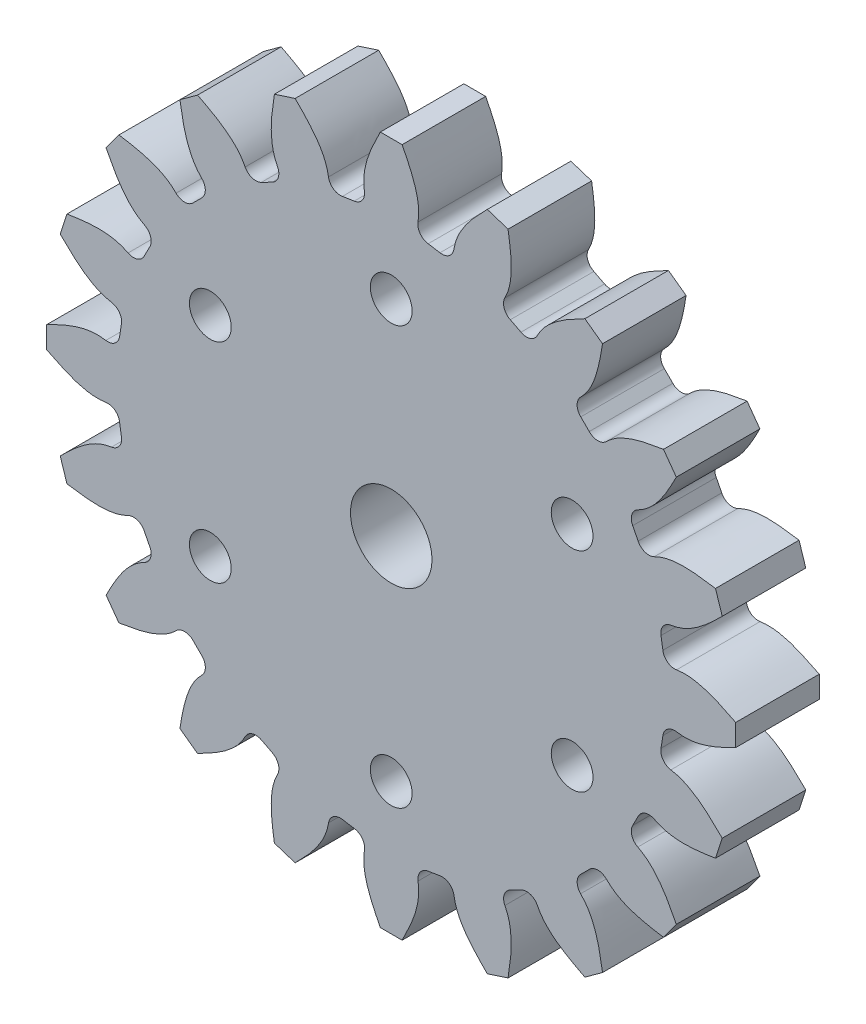
SolidWorks part; units mm, degrees
ref_plane "Plan de face" through (0, 0, 0) normal (0, 0, 1) x (1, 0, 0)
ref_plane "Plan de dessus" through (0, 0, 0) normal (0, 1, 0) x (1, 0, 0)
ref_plane "Plan de droite" through (0, 0, 0) normal (1, 0, 0) x (0, 0, -1)
sketch "Esquisse1" plane through (0, 0, 0) normal (0, 0, 1) x (1, 0, 0)
  line L0 (15.1743, 19.5525) -> (13.9064, 20.4737)
  line L1 (9.3174, 17.3431) -> (8.5503, 17.7339)
  line L2 (8.3896, 23.2847) -> (6.8991, 23.769)
  line L3 (3.5021, 19.3735) -> (2.6518, 19.5081)
  line L4 (0.7836, 24.7376) -> (-0.7836, 24.7376)
  line L5 (-2.656, 19.5075) -> (-3.5064, 19.3727)
  line L6 (-6.8991, 23.769) -> (-8.3896, 23.2847)
  line L7 (-8.5542, 17.732) -> (-9.3212, 17.341)
  line L8 (-13.9064, 20.4737) -> (-15.1743, 19.5525)
  line L9 (-13.615, 14.2207) -> (-14.2237, 13.6119)
  line L10 (-19.5525, 15.1743) -> (-20.4737, 13.9064)
  line L11 (-17.3431, 9.3174) -> (-17.7339, 8.5503)
  line L12 (-23.2847, 8.3896) -> (-23.769, 6.8991)
  line L13 (-19.3735, 3.5021) -> (-19.5081, 2.6518)
  line L14 (-24.7376, 0.7836) -> (-24.7376, -0.7836)
  line L15 (-19.5075, -2.656) -> (-19.3727, -3.5064)
  line L16 (-23.769, -6.8991) -> (-23.2847, -8.3896)
  line L17 (-17.732, -8.5542) -> (-17.341, -9.3212)
  line L18 (-20.4737, -13.9064) -> (-19.5525, -15.1743)
  line L19 (-14.2207, -13.615) -> (-13.6119, -14.2237)
  line L20 (-15.1743, -19.5525) -> (-13.9064, -20.4737)
  line L21 (-9.3174, -17.3431) -> (-8.5503, -17.7339)
  line L22 (-8.3896, -23.2847) -> (-6.8991, -23.769)
  line L23 (-3.5021, -19.3735) -> (-2.6518, -19.5081)
  line L24 (-0.7836, -24.7376) -> (0.7836, -24.7376)
  line L25 (2.656, -19.5075) -> (3.5064, -19.3727)
  line L26 (6.8991, -23.769) -> (8.3896, -23.2847)
  line L27 (8.5542, -17.732) -> (9.3212, -17.341)
  line L28 (13.9064, -20.4737) -> (15.1743, -19.5525)
  line L29 (13.615, -14.2207) -> (14.2237, -13.6119)
  line L30 (19.5525, -15.1743) -> (20.4737, -13.9064)
  line L31 (17.3431, -9.3174) -> (17.7339, -8.5503)
  line L32 (23.2847, -8.3896) -> (23.769, -6.8991)
  line L33 (19.3735, -3.5021) -> (19.5081, -2.6518)
  line L34 (24.7376, -0.7836) -> (24.7376, 0.7836)
  line L35 (19.5075, 2.656) -> (19.3727, 3.5064)
  line L36 (23.769, 6.8991) -> (23.2847, 8.3896)
  line L37 (17.732, 8.5542) -> (17.341, 9.3212)
  line L38 (20.4737, 13.9064) -> (19.5525, 15.1743)
  line L39 (14.2207, 13.615) -> (13.6119, 14.2237)
  arc A7 (3.5021, 19.3735) -> (4.4983, 20.0787) centre (3.6542, 20.2149) ccw
  arc A9 (8.1621, 18.8967) -> (8.5503, 17.7339) centre (8.9216, 18.504) ccw
  arc A11 (9.3174, 17.3431) -> (10.4828, 17.706) centre (9.7221, 18.0963) ccw
  arc A13 (13.602, 15.4496) -> (13.6119, 14.2237) centre (14.203, 14.8414) ccw
  arc A15 (14.2207, 13.615) -> (15.4412, 13.6) centre (14.8383, 14.2063) ccw
  arc A17 (17.7105, 10.4901) -> (17.341, 9.3212) centre (18.0941, 9.7261) ccw
  arc A19 (17.732, 8.5542) -> (18.8881, 8.1628) centre (18.5021, 8.9257) ccw
  arc A21 (20.0853, 4.5039) -> (19.3727, 3.5064) centre (20.2141, 3.6586) ccw
  arc A23 (19.5075, 2.656) -> (20.4861, 1.9265) centre (20.3547, 2.7714) ccw
  arc A25 (20.494, -1.9233) -> (19.5081, -2.6518) centre (20.3553, -2.7669) ccw
  arc A27 (19.3735, -3.5021) -> (20.0787, -4.4983) centre (20.2149, -3.6542) ccw
  arc A29 (18.8967, -8.1621) -> (17.7339, -8.5503) centre (18.504, -8.9216) ccw
  arc A31 (17.3431, -9.3174) -> (17.706, -10.4828) centre (18.0963, -9.7221) ccw
  arc A33 (15.4496, -13.602) -> (14.2237, -13.6119) centre (14.8414, -14.203) ccw
  arc A35 (13.615, -14.2207) -> (13.6, -15.4412) centre (14.2063, -14.8383) ccw
  arc A37 (10.4901, -17.7105) -> (9.3212, -17.341) centre (9.7261, -18.0941) ccw
  arc A39 (8.5542, -17.732) -> (8.1628, -18.8881) centre (8.9257, -18.5021) ccw
  arc A41 (4.5039, -20.0853) -> (3.5064, -19.3727) centre (3.6586, -20.2141) ccw
  arc A43 (2.656, -19.5075) -> (1.9265, -20.4861) centre (2.7714, -20.3547) ccw
  arc A45 (-1.9233, -20.494) -> (-2.6518, -19.5081) centre (-2.7669, -20.3553) ccw
  arc A47 (-3.5021, -19.3735) -> (-4.4983, -20.0787) centre (-3.6542, -20.2149) ccw
  arc A49 (-8.1621, -18.8967) -> (-8.5503, -17.7339) centre (-8.9216, -18.504) ccw
  arc A51 (-9.3174, -17.3431) -> (-10.4828, -17.706) centre (-9.7221, -18.0963) ccw
  arc A53 (-13.602, -15.4496) -> (-13.6119, -14.2237) centre (-14.203, -14.8414) ccw
  arc A55 (-14.2207, -13.615) -> (-15.4412, -13.6) centre (-14.8383, -14.2063) ccw
  arc A57 (-17.7105, -10.4901) -> (-17.341, -9.3212) centre (-18.0941, -9.7261) ccw
  arc A59 (-17.732, -8.5542) -> (-18.8881, -8.1628) centre (-18.5021, -8.9257) ccw
  arc A61 (-20.0853, -4.5039) -> (-19.3727, -3.5064) centre (-20.2141, -3.6586) ccw
  arc A63 (-19.5075, -2.656) -> (-20.4861, -1.9265) centre (-20.3547, -2.7714) ccw
  arc A65 (-20.494, 1.9233) -> (-19.5081, 2.6518) centre (-20.3553, 2.7669) ccw
  arc A67 (-19.3735, 3.5021) -> (-20.0787, 4.4983) centre (-20.2149, 3.6542) ccw
  arc A69 (-18.8967, 8.1621) -> (-17.7339, 8.5503) centre (-18.504, 8.9216) ccw
  arc A71 (-17.3431, 9.3174) -> (-17.706, 10.4828) centre (-18.0963, 9.7221) ccw
  arc A73 (-15.4496, 13.602) -> (-14.2237, 13.6119) centre (-14.8414, 14.203) ccw
  arc A75 (-13.615, 14.2207) -> (-13.6, 15.4412) centre (-14.2063, 14.8383) ccw
  arc A77 (-10.4901, 17.7105) -> (-9.3212, 17.341) centre (-9.7261, 18.0941) ccw
  arc A79 (-8.5542, 17.732) -> (-8.1628, 18.8881) centre (-8.9257, 18.5021) ccw
  arc A81 (-4.5039, 20.0853) -> (-3.5064, 19.3727) centre (-3.6586, 20.2141) ccw
  arc A83 (-2.656, 19.5075) -> (-1.9265, 20.4861) centre (-2.7714, 20.3547) ccw
  arc A85 (1.9233, 20.494) -> (2.6518, 19.5081) centre (2.7669, 20.3553) ccw
  spline S0 degree 3 poles (8.1621, 18.8967) (8.2478, 19.0624) (8.5054, 19.6524) (8.7113, 21.1682) (8.5154, 22.4568) (8.3896, 23.2847) knots 0.425084 0.425084 0.425084 0.425084 0.498147 0.677544 1 1 1 1
  spline S1 degree 3 poles (6.8991, 23.769) (6.3099, 23.1731) (5.3928, 22.2457) (4.6724, 20.8967) (4.5284, 20.2654) (4.4983, 20.0787) knots 0 0 0 0 0.322456 0.501853 0.575753 0.575753 0.575753 0.575753
  spline S2 degree 3 poles (13.602, 15.4496) (13.7347, 15.5807) (14.1621, 16.0622) (14.8262, 17.4402) (15.0382, 18.7262) (15.1743, 19.5525) knots 0.425084 0.425084 0.425084 0.425084 0.498147 0.677544 1 1 1 1
  spline S3 degree 3 poles (13.9064, 20.4737) (13.1619, 20.0891) (12.0032, 19.4904) (10.9011, 18.4301) (10.5691, 17.8742) (10.4828, 17.706) knots 0 0 0 0 0.322456 0.501853 0.575753 0.575753 0.575753 0.575753
  spline S4 degree 3 poles (17.7105, 10.4901) (17.8772, 10.5738) (18.4324, 10.8998) (19.4899, 12.0051) (20.0889, 13.1626) (20.4737, 13.9064) knots 0.425084 0.425084 0.425084 0.425084 0.498147 0.677544 1 1 1 1
  spline S5 degree 3 poles (19.5525, 15.1743) (18.7256, 15.0386) (17.4386, 14.8273) (16.0628, 14.1594) (15.5753, 13.7333) (15.4412, 13.6) knots 0 0 0 0 0.322456 0.501853 0.575753 0.575753 0.575753 0.575753
  spline S6 degree 3 poles (20.0853, 4.5039) (20.2697, 4.532) (20.8985, 4.6704) (22.2458, 5.3948) (23.1731, 6.3106) (23.769, 6.8991) knots 0.425084 0.425084 0.425084 0.425084 0.498147 0.677544 1 1 1 1
  spline S7 degree 3 poles (23.2847, 8.3896) (22.4563, 8.516) (21.1669, 8.7128) (19.6521, 8.5028) (19.0568, 8.2482) (18.8881, 8.1628) knots 0 0 0 0 0.322456 0.501853 0.575753 0.575753 0.575753 0.575753
  spline S8 degree 3 poles (20.494, -1.9233) (20.6781, -1.9535) (21.3189, -2.0162) (22.8241, -1.7436) (23.9891, -1.1591) (24.7376, -0.7836) knots 0.425084 0.425084 0.425084 0.425084 0.498147 0.677544 1 1 1 1
  spline S9 degree 3 poles (24.7376, 0.7836) (23.9888, 1.1598) (22.8234, 1.7454) (21.3178, 2.0138) (20.6729, 1.9556) (20.4861, 1.9265) knots 0 0 0 0 0.322456 0.501853 0.575753 0.575753 0.575753 0.575753
  spline S10 degree 3 poles (18.8967, -8.1621) (19.0624, -8.2478) (19.6524, -8.5054) (21.1682, -8.7113) (22.4568, -8.5154) (23.2847, -8.3896) knots 0.425084 0.425084 0.425084 0.425084 0.498147 0.677544 1 1 1 1
  spline S11 degree 3 poles (23.769, -6.8991) (23.1731, -6.3099) (22.2457, -5.3928) (20.8967, -4.6724) (20.2654, -4.5284) (20.0787, -4.4983) knots 0 0 0 0 0.322456 0.501853 0.575753 0.575753 0.575753 0.575753
  spline S12 degree 3 poles (15.4496, -13.602) (15.5807, -13.7347) (16.0622, -14.1621) (17.4402, -14.8262) (18.7262, -15.0382) (19.5525, -15.1743) knots 0.425084 0.425084 0.425084 0.425084 0.498147 0.677544 1 1 1 1
  spline S13 degree 3 poles (20.4737, -13.9064) (20.0891, -13.1619) (19.4904, -12.0032) (18.4301, -10.9011) (17.8742, -10.5691) (17.706, -10.4828) knots 0 0 0 0 0.322456 0.501853 0.575753 0.575753 0.575753 0.575753
  spline S14 degree 3 poles (10.4901, -17.7105) (10.5738, -17.8772) (10.8998, -18.4324) (12.0051, -19.4899) (13.1626, -20.0889) (13.9064, -20.4737) knots 0.425084 0.425084 0.425084 0.425084 0.498147 0.677544 1 1 1 1
  spline S15 degree 3 poles (15.1743, -19.5525) (15.0386, -18.7256) (14.8273, -17.4386) (14.1594, -16.0628) (13.7333, -15.5753) (13.6, -15.4412) knots 0 0 0 0 0.322456 0.501853 0.575753 0.575753 0.575753 0.575753
  spline S16 degree 3 poles (4.5039, -20.0853) (4.532, -20.2697) (4.6704, -20.8985) (5.3948, -22.2458) (6.3106, -23.1731) (6.8991, -23.769) knots 0.425084 0.425084 0.425084 0.425084 0.498147 0.677544 1 1 1 1
  spline S17 degree 3 poles (8.3896, -23.2847) (8.516, -22.4563) (8.7128, -21.1669) (8.5028, -19.6521) (8.2482, -19.0568) (8.1628, -18.8881) knots 0 0 0 0 0.322456 0.501853 0.575753 0.575753 0.575753 0.575753
  spline S18 degree 3 poles (-1.9233, -20.494) (-1.9535, -20.6781) (-2.0162, -21.3189) (-1.7436, -22.8241) (-1.1591, -23.9891) (-0.7836, -24.7376) knots 0.425084 0.425084 0.425084 0.425084 0.498147 0.677544 1 1 1 1
  spline S19 degree 3 poles (0.7836, -24.7376) (1.1598, -23.9888) (1.7454, -22.8234) (2.0138, -21.3178) (1.9556, -20.6729) (1.9265, -20.4861) knots 0 0 0 0 0.322456 0.501853 0.575753 0.575753 0.575753 0.575753
  spline S20 degree 3 poles (-8.1621, -18.8967) (-8.2478, -19.0624) (-8.5054, -19.6524) (-8.7113, -21.1682) (-8.5154, -22.4568) (-8.3896, -23.2847) knots 0.425084 0.425084 0.425084 0.425084 0.498147 0.677544 1 1 1 1
  spline S21 degree 3 poles (-6.8991, -23.769) (-6.3099, -23.1731) (-5.3928, -22.2457) (-4.6724, -20.8967) (-4.5284, -20.2654) (-4.4983, -20.0787) knots 0 0 0 0 0.322456 0.501853 0.575753 0.575753 0.575753 0.575753
  spline S22 degree 3 poles (-13.602, -15.4496) (-13.7347, -15.5807) (-14.1621, -16.0622) (-14.8262, -17.4402) (-15.0382, -18.7262) (-15.1743, -19.5525) knots 0.425084 0.425084 0.425084 0.425084 0.498147 0.677544 1 1 1 1
  spline S23 degree 3 poles (-13.9064, -20.4737) (-13.1619, -20.0891) (-12.0032, -19.4904) (-10.9011, -18.4301) (-10.5691, -17.8742) (-10.4828, -17.706) knots 0 0 0 0 0.322456 0.501853 0.575753 0.575753 0.575753 0.575753
  spline S24 degree 3 poles (-17.7105, -10.4901) (-17.8772, -10.5738) (-18.4324, -10.8998) (-19.4899, -12.0051) (-20.0889, -13.1626) (-20.4737, -13.9064) knots 0.425084 0.425084 0.425084 0.425084 0.498147 0.677544 1 1 1 1
  spline S25 degree 3 poles (-19.5525, -15.1743) (-18.7256, -15.0386) (-17.4386, -14.8273) (-16.0628, -14.1594) (-15.5753, -13.7333) (-15.4412, -13.6) knots 0 0 0 0 0.322456 0.501853 0.575753 0.575753 0.575753 0.575753
  spline S26 degree 3 poles (-20.0853, -4.5039) (-20.2697, -4.532) (-20.8985, -4.6704) (-22.2458, -5.3948) (-23.1731, -6.3106) (-23.769, -6.8991) knots 0.425084 0.425084 0.425084 0.425084 0.498147 0.677544 1 1 1 1
  spline S27 degree 3 poles (-23.2847, -8.3896) (-22.4563, -8.516) (-21.1669, -8.7128) (-19.6521, -8.5028) (-19.0568, -8.2482) (-18.8881, -8.1628) knots 0 0 0 0 0.322456 0.501853 0.575753 0.575753 0.575753 0.575753
  spline S28 degree 3 poles (-20.494, 1.9233) (-20.6781, 1.9535) (-21.3189, 2.0162) (-22.8241, 1.7436) (-23.9891, 1.1591) (-24.7376, 0.7836) knots 0.425084 0.425084 0.425084 0.425084 0.498147 0.677544 1 1 1 1
  spline S29 degree 3 poles (-24.7376, -0.7836) (-23.9888, -1.1598) (-22.8234, -1.7454) (-21.3178, -2.0138) (-20.6729, -1.9556) (-20.4861, -1.9265) knots 0 0 0 0 0.322456 0.501853 0.575753 0.575753 0.575753 0.575753
  spline S30 degree 3 poles (-18.8967, 8.1621) (-19.0624, 8.2478) (-19.6524, 8.5054) (-21.1682, 8.7113) (-22.4568, 8.5154) (-23.2847, 8.3896) knots 0.425084 0.425084 0.425084 0.425084 0.498147 0.677544 1 1 1 1
  spline S31 degree 3 poles (-23.769, 6.8991) (-23.1731, 6.3099) (-22.2457, 5.3928) (-20.8967, 4.6724) (-20.2654, 4.5284) (-20.0787, 4.4983) knots 0 0 0 0 0.322456 0.501853 0.575753 0.575753 0.575753 0.575753
  spline S32 degree 3 poles (-15.4496, 13.602) (-15.5807, 13.7347) (-16.0622, 14.1621) (-17.4402, 14.8262) (-18.7262, 15.0382) (-19.5525, 15.1743) knots 0.425084 0.425084 0.425084 0.425084 0.498147 0.677544 1 1 1 1
  spline S33 degree 3 poles (-20.4737, 13.9064) (-20.0891, 13.1619) (-19.4904, 12.0032) (-18.4301, 10.9011) (-17.8742, 10.5691) (-17.706, 10.4828) knots 0 0 0 0 0.322456 0.501853 0.575753 0.575753 0.575753 0.575753
  spline S34 degree 3 poles (-10.4901, 17.7105) (-10.5738, 17.8772) (-10.8998, 18.4324) (-12.0051, 19.4899) (-13.1626, 20.0889) (-13.9064, 20.4737) knots 0.425084 0.425084 0.425084 0.425084 0.498147 0.677544 1 1 1 1
  spline S35 degree 3 poles (-15.1743, 19.5525) (-15.0386, 18.7256) (-14.8273, 17.4386) (-14.1594, 16.0628) (-13.7333, 15.5753) (-13.6, 15.4412) knots 0 0 0 0 0.322456 0.501853 0.575753 0.575753 0.575753 0.575753
  spline S36 degree 3 poles (-4.5039, 20.0853) (-4.532, 20.2697) (-4.6704, 20.8985) (-5.3948, 22.2458) (-6.3106, 23.1731) (-6.8991, 23.769) knots 0.425084 0.425084 0.425084 0.425084 0.498147 0.677544 1 1 1 1
  spline S37 degree 3 poles (-8.3896, 23.2847) (-8.516, 22.4563) (-8.7128, 21.1669) (-8.5028, 19.6521) (-8.2482, 19.0568) (-8.1628, 18.8881) knots 0 0 0 0 0.322456 0.501853 0.575753 0.575753 0.575753 0.575753
  spline S38 degree 3 poles (1.9233, 20.494) (1.9535, 20.6781) (2.0162, 21.3189) (1.7436, 22.8241) (1.1591, 23.9891) (0.7836, 24.7376) knots 0.425084 0.425084 0.425084 0.425084 0.498147 0.677544 1 1 1 1
  spline S39 degree 3 poles (-0.7836, 24.7376) (-1.1598, 23.9888) (-1.7454, 22.8234) (-2.0138, 21.3178) (-1.9556, 20.6729) (-1.9265, 20.4861) knots 0 0 0 0 0.322456 0.501853 0.575753 0.575753 0.575753 0.575753
  spline S40 degree 3 poles (6.8991, 23.769) (6.3099, 23.1731) (5.3928, 22.2457) (4.6724, 20.8967) (4.5284, 20.2654) (4.4983, 20.0787) knots 0 0 0 0 0.322456 0.501853 0.575753 0.575753 0.575753 0.575753
  spline S41 degree 3 poles (8.1621, 18.8967) (8.2478, 19.0624) (8.5054, 19.6524) (8.7113, 21.1682) (8.5154, 22.4568) (8.3896, 23.2847) knots 0.425084 0.425084 0.425084 0.425084 0.498147 0.677544 1 1 1 1
  spline S42 degree 3 poles (13.9064, 20.4737) (13.1619, 20.0891) (12.0032, 19.4904) (10.9011, 18.4301) (10.5691, 17.8742) (10.4828, 17.706) knots 0 0 0 0 0.322456 0.501853 0.575753 0.575753 0.575753 0.575753
  spline S43 degree 3 poles (13.602, 15.4496) (13.7347, 15.5807) (14.1621, 16.0622) (14.8262, 17.4402) (15.0382, 18.7262) (15.1743, 19.5525) knots 0.425084 0.425084 0.425084 0.425084 0.498147 0.677544 1 1 1 1
  spline S44 degree 3 poles (19.5525, 15.1743) (18.7256, 15.0386) (17.4386, 14.8273) (16.0628, 14.1594) (15.5753, 13.7333) (15.4412, 13.6) knots 0 0 0 0 0.322456 0.501853 0.575753 0.575753 0.575753 0.575753
  spline S45 degree 3 poles (17.7105, 10.4901) (17.8772, 10.5738) (18.4324, 10.8998) (19.4899, 12.0051) (20.0889, 13.1626) (20.4737, 13.9064) knots 0.425084 0.425084 0.425084 0.425084 0.498147 0.677544 1 1 1 1
  spline S46 degree 3 poles (23.2847, 8.3896) (22.4563, 8.516) (21.1669, 8.7128) (19.6521, 8.5028) (19.0568, 8.2482) (18.8881, 8.1628) knots 0 0 0 0 0.322456 0.501853 0.575753 0.575753 0.575753 0.575753
  spline S47 degree 3 poles (20.0853, 4.5039) (20.2697, 4.532) (20.8985, 4.6704) (22.2458, 5.3948) (23.1731, 6.3106) (23.769, 6.8991) knots 0.425084 0.425084 0.425084 0.425084 0.498147 0.677544 1 1 1 1
  spline S48 degree 3 poles (24.7376, 0.7836) (23.9888, 1.1598) (22.8234, 1.7454) (21.3178, 2.0138) (20.6729, 1.9556) (20.4861, 1.9265) knots 0 0 0 0 0.322456 0.501853 0.575753 0.575753 0.575753 0.575753
  spline S49 degree 3 poles (20.494, -1.9233) (20.6781, -1.9535) (21.3189, -2.0162) (22.8241, -1.7436) (23.9891, -1.1591) (24.7376, -0.7836) knots 0.425084 0.425084 0.425084 0.425084 0.498147 0.677544 1 1 1 1
  spline S50 degree 3 poles (23.769, -6.8991) (23.1731, -6.3099) (22.2457, -5.3928) (20.8967, -4.6724) (20.2654, -4.5284) (20.0787, -4.4983) knots 0 0 0 0 0.322456 0.501853 0.575753 0.575753 0.575753 0.575753
  spline S51 degree 3 poles (18.8967, -8.1621) (19.0624, -8.2478) (19.6524, -8.5054) (21.1682, -8.7113) (22.4568, -8.5154) (23.2847, -8.3896) knots 0.425084 0.425084 0.425084 0.425084 0.498147 0.677544 1 1 1 1
  spline S52 degree 3 poles (20.4737, -13.9064) (20.0891, -13.1619) (19.4904, -12.0032) (18.4301, -10.9011) (17.8742, -10.5691) (17.706, -10.4828) knots 0 0 0 0 0.322456 0.501853 0.575753 0.575753 0.575753 0.575753
  spline S53 degree 3 poles (15.4496, -13.602) (15.5807, -13.7347) (16.0622, -14.1621) (17.4402, -14.8262) (18.7262, -15.0382) (19.5525, -15.1743) knots 0.425084 0.425084 0.425084 0.425084 0.498147 0.677544 1 1 1 1
  spline S54 degree 3 poles (15.1743, -19.5525) (15.0386, -18.7256) (14.8273, -17.4386) (14.1594, -16.0628) (13.7333, -15.5753) (13.6, -15.4412) knots 0 0 0 0 0.322456 0.501853 0.575753 0.575753 0.575753 0.575753
  spline S55 degree 3 poles (10.4901, -17.7105) (10.5738, -17.8772) (10.8998, -18.4324) (12.0051, -19.4899) (13.1626, -20.0889) (13.9064, -20.4737) knots 0.425084 0.425084 0.425084 0.425084 0.498147 0.677544 1 1 1 1
  spline S56 degree 3 poles (8.3896, -23.2847) (8.516, -22.4563) (8.7128, -21.1669) (8.5028, -19.6521) (8.2482, -19.0568) (8.1628, -18.8881) knots 0 0 0 0 0.322456 0.501853 0.575753 0.575753 0.575753 0.575753
  spline S57 degree 3 poles (4.5039, -20.0853) (4.532, -20.2697) (4.6704, -20.8985) (5.3948, -22.2458) (6.3106, -23.1731) (6.8991, -23.769) knots 0.425084 0.425084 0.425084 0.425084 0.498147 0.677544 1 1 1 1
  spline S58 degree 3 poles (0.7836, -24.7376) (1.1598, -23.9888) (1.7454, -22.8234) (2.0138, -21.3178) (1.9556, -20.6729) (1.9265, -20.4861) knots 0 0 0 0 0.322456 0.501853 0.575753 0.575753 0.575753 0.575753
  spline S59 degree 3 poles (-1.9233, -20.494) (-1.9535, -20.6781) (-2.0162, -21.3189) (-1.7436, -22.8241) (-1.1591, -23.9891) (-0.7836, -24.7376) knots 0.425084 0.425084 0.425084 0.425084 0.498147 0.677544 1 1 1 1
  spline S60 degree 3 poles (-6.8991, -23.769) (-6.3099, -23.1731) (-5.3928, -22.2457) (-4.6724, -20.8967) (-4.5284, -20.2654) (-4.4983, -20.0787) knots 0 0 0 0 0.322456 0.501853 0.575753 0.575753 0.575753 0.575753
  spline S61 degree 3 poles (-8.1621, -18.8967) (-8.2478, -19.0624) (-8.5054, -19.6524) (-8.7113, -21.1682) (-8.5154, -22.4568) (-8.3896, -23.2847) knots 0.425084 0.425084 0.425084 0.425084 0.498147 0.677544 1 1 1 1
  spline S62 degree 3 poles (-13.9064, -20.4737) (-13.1619, -20.0891) (-12.0032, -19.4904) (-10.9011, -18.4301) (-10.5691, -17.8742) (-10.4828, -17.706) knots 0 0 0 0 0.322456 0.501853 0.575753 0.575753 0.575753 0.575753
  spline S63 degree 3 poles (-13.602, -15.4496) (-13.7347, -15.5807) (-14.1621, -16.0622) (-14.8262, -17.4402) (-15.0382, -18.7262) (-15.1743, -19.5525) knots 0.425084 0.425084 0.425084 0.425084 0.498147 0.677544 1 1 1 1
  spline S64 degree 3 poles (-19.5525, -15.1743) (-18.7256, -15.0386) (-17.4386, -14.8273) (-16.0628, -14.1594) (-15.5753, -13.7333) (-15.4412, -13.6) knots 0 0 0 0 0.322456 0.501853 0.575753 0.575753 0.575753 0.575753
  spline S65 degree 3 poles (-17.7105, -10.4901) (-17.8772, -10.5738) (-18.4324, -10.8998) (-19.4899, -12.0051) (-20.0889, -13.1626) (-20.4737, -13.9064) knots 0.425084 0.425084 0.425084 0.425084 0.498147 0.677544 1 1 1 1
  spline S66 degree 3 poles (-23.2847, -8.3896) (-22.4563, -8.516) (-21.1669, -8.7128) (-19.6521, -8.5028) (-19.0568, -8.2482) (-18.8881, -8.1628) knots 0 0 0 0 0.322456 0.501853 0.575753 0.575753 0.575753 0.575753
  spline S67 degree 3 poles (-20.0853, -4.5039) (-20.2697, -4.532) (-20.8985, -4.6704) (-22.2458, -5.3948) (-23.1731, -6.3106) (-23.769, -6.8991) knots 0.425084 0.425084 0.425084 0.425084 0.498147 0.677544 1 1 1 1
  spline S68 degree 3 poles (-24.7376, -0.7836) (-23.9888, -1.1598) (-22.8234, -1.7454) (-21.3178, -2.0138) (-20.6729, -1.9556) (-20.4861, -1.9265) knots 0 0 0 0 0.322456 0.501853 0.575753 0.575753 0.575753 0.575753
  spline S69 degree 3 poles (-20.494, 1.9233) (-20.6781, 1.9535) (-21.3189, 2.0162) (-22.8241, 1.7436) (-23.9891, 1.1591) (-24.7376, 0.7836) knots 0.425084 0.425084 0.425084 0.425084 0.498147 0.677544 1 1 1 1
  spline S70 degree 3 poles (-23.769, 6.8991) (-23.1731, 6.3099) (-22.2457, 5.3928) (-20.8967, 4.6724) (-20.2654, 4.5284) (-20.0787, 4.4983) knots 0 0 0 0 0.322456 0.501853 0.575753 0.575753 0.575753 0.575753
  spline S71 degree 3 poles (-18.8967, 8.1621) (-19.0624, 8.2478) (-19.6524, 8.5054) (-21.1682, 8.7113) (-22.4568, 8.5154) (-23.2847, 8.3896) knots 0.425084 0.425084 0.425084 0.425084 0.498147 0.677544 1 1 1 1
  spline S72 degree 3 poles (-20.4737, 13.9064) (-20.0891, 13.1619) (-19.4904, 12.0032) (-18.4301, 10.9011) (-17.8742, 10.5691) (-17.706, 10.4828) knots 0 0 0 0 0.322456 0.501853 0.575753 0.575753 0.575753 0.575753
  spline S73 degree 3 poles (-15.4496, 13.602) (-15.5807, 13.7347) (-16.0622, 14.1621) (-17.4402, 14.8262) (-18.7262, 15.0382) (-19.5525, 15.1743) knots 0.425084 0.425084 0.425084 0.425084 0.498147 0.677544 1 1 1 1
  spline S74 degree 3 poles (-15.1743, 19.5525) (-15.0386, 18.7256) (-14.8273, 17.4386) (-14.1594, 16.0628) (-13.7333, 15.5753) (-13.6, 15.4412) knots 0 0 0 0 0.322456 0.501853 0.575753 0.575753 0.575753 0.575753
  spline S75 degree 3 poles (-10.4901, 17.7105) (-10.5738, 17.8772) (-10.8998, 18.4324) (-12.0051, 19.4899) (-13.1626, 20.0889) (-13.9064, 20.4737) knots 0.425084 0.425084 0.425084 0.425084 0.498147 0.677544 1 1 1 1
  spline S76 degree 3 poles (-8.3896, 23.2847) (-8.516, 22.4563) (-8.7128, 21.1669) (-8.5028, 19.6521) (-8.2482, 19.0568) (-8.1628, 18.8881) knots 0 0 0 0 0.322456 0.501853 0.575753 0.575753 0.575753 0.575753
  spline S77 degree 3 poles (-4.5039, 20.0853) (-4.532, 20.2697) (-4.6704, 20.8985) (-5.3948, 22.2458) (-6.3106, 23.1731) (-6.8991, 23.769) knots 0.425084 0.425084 0.425084 0.425084 0.498147 0.677544 1 1 1 1
  spline S78 degree 3 poles (-0.7836, 24.7376) (-1.1598, 23.9888) (-1.7454, 22.8234) (-2.0138, 21.3178) (-1.9556, 20.6729) (-1.9265, 20.4861) knots 0 0 0 0 0.322456 0.501853 0.575753 0.575753 0.575753 0.575753
  spline S79 degree 3 poles (1.9233, 20.494) (1.9535, 20.6781) (2.0162, 21.3189) (1.7436, 22.8241) (1.1591, 23.9891) (0.7836, 24.7376) knots 0.425084 0.425084 0.425084 0.425084 0.498147 0.677544 1 1 1 1
extrude "Extrusion1" add sketch "Esquisse1" along normal blind 6 contours L4 S39 A83 L5 A81 S36 L6 S37 A79 L7 A77 S34 L8 S35 A75 L9 A73 S32 L10 S33 A71 L11 A69 S30 L12 S31 A67 L13 A65 S28 L14 S29 A63 L15 A61 S26 L16 S27 A59 L17 A57 S24 L18 S25 A55 L19 A53 S22 L20 S23 A51
sketch "Esquisse2" plane through (0, 0, 0) normal (0, 0, -1) x (-1, 0, 0)
  line L0 (0, 0) -> (0, 27.4223) construction
  circle A0 centre (0, 14.7443) radius 1.5
  circle A1 centre (12.9904, 7.2443) radius 1.5
  circle A2 centre (12.9904, -7.7557) radius 1.5
  circle A3 centre (0, -15.2557) radius 1.5
  circle A4 centre (-12.9904, -7.7557) radius 1.5
  circle A5 centre (-12.9904, 7.2443) radius 1.5
  circle A6 centre (0, 0) radius 2.925
  dimension "D1" = 3
  dimension "D2" = 5.85
  dimension "D3" = 15
extrude "Extrusion2" cut sketch "Esquisse2" against normal through all
